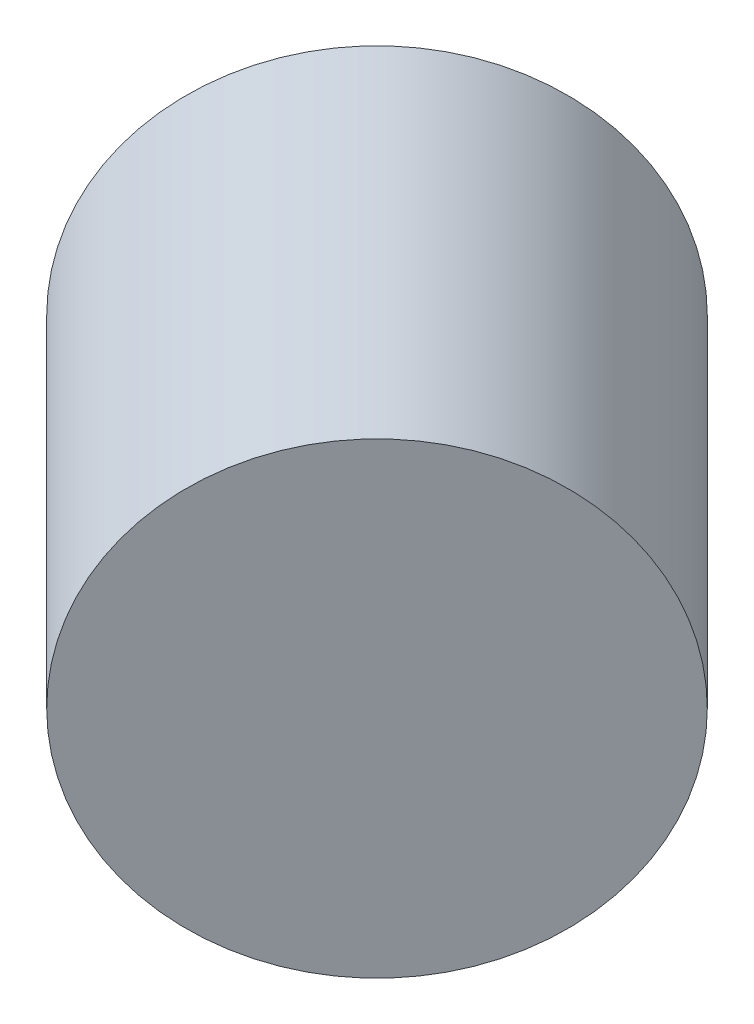
SolidWorks part; units mm, degrees
ref_plane "Front Plane" through (0, 0, 0) normal (0, 0, 1) x (1, 0, 0)
ref_plane "Top Plane" through (0, 0, 0) normal (0, 1, 0) x (1, 0, 0)
ref_plane "Right Plane" through (0, 0, 0) normal (1, 0, 0) x (0, 0, -1)
ref_plane "Plane1" through (-155.8554, 0, -155.8554) normal (-0.7071, 0, -0.7071) x (-0.7071, 0, 0.7071)
sketch "Sketch1" plane through (-155.8554, 0, -155.8554) normal (-0.7071, 0, -0.7071) x (-0.7071, 0, 0.7071)
  circle B0 centre (-558.5079, -7.5) radius 49
sketch_block_instance "Block1-1"
sketch_block "Block1"
extrude "Boss-Extrude1" add sketch "Sketch1" against normal blind 101
